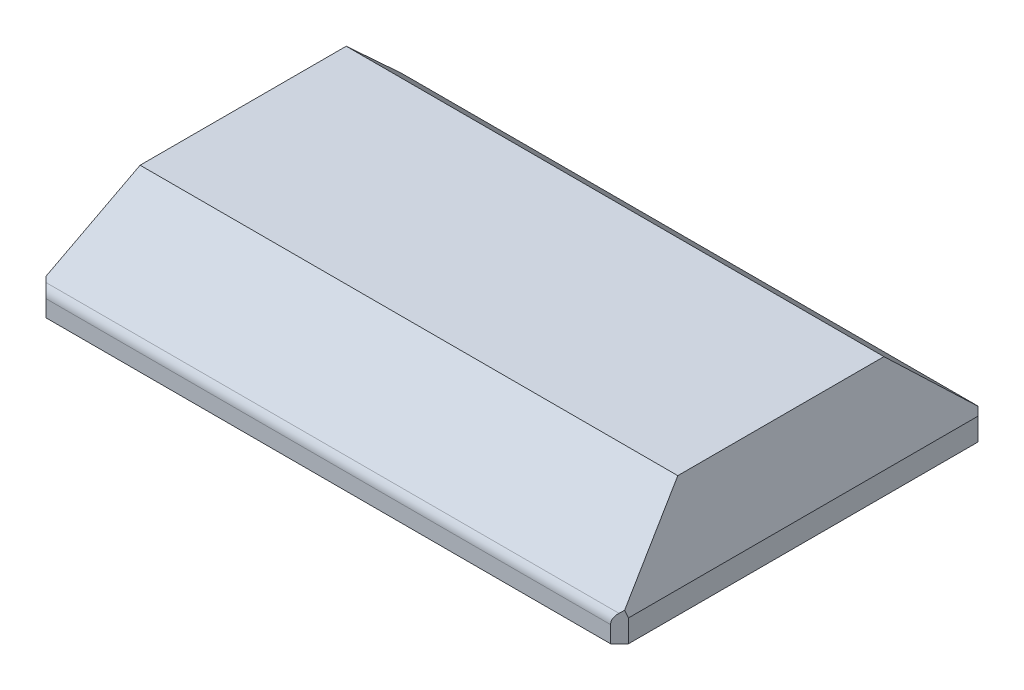
SolidWorks part; units mm, degrees
ref_plane "Front Plane" through (0, 0, 0) normal (0, 0, 1) x (1, 0, 0)
ref_plane "Top Plane" through (0, 0, 0) normal (0, 1, 0) x (1, 0, 0)
ref_plane "Right Plane" through (0, 0, 0) normal (1, 0, 0) x (0, 0, -1)
sketch "Sketch1" plane through (0, 0, 0) normal (0, 1, 0) x (1, 0, 0)
  line L1 (-65, -41) -> (65, -41)
  line L2 (-65, -41) -> (-65, 41)
  line L3 (-65, 41) -> (65, 41)
  line L4 (65, -41) -> (65, 41)
  line L5 (-65, -41) -> (65, 41) construction
  line L6 (-65, 41) -> (65, -41) construction
  point P0 (0, 0)
  dimension "D1" = 130
  dimension "D2" = 82
ref_plane "Plane1" through (0, 22, 0) normal (0, 1, 0) x (1, 0, 0)
sketch "Sketch2" plane through (0, 22, 0) normal (0, 1, 0) x (1, 0, 0)
  line L1 (-60, -23) -> (60, -23)
  line L2 (-60, -23) -> (-60, 23)
  line L3 (-60, 23) -> (60, 23)
  line L4 (60, -23) -> (60, 23)
  line L5 (-60, -23) -> (60, 23) construction
  line L6 (-60, 23) -> (60, -23) construction
  point P0 (0, 0)
  dimension "D1" = 46
  dimension "D2" = 120
extrude "Boss-Extrude1" add sketch "Sketch1" along normal blind 5
sketch "Sketch3" plane through (0, 5, 0) normal (0, 1, 0) x (1, 0, 0)
  line L4 (65, -41) -> (65, 41)
  line L5 (65, 41) -> (-65, 41)
  line L6 (-65, 41) -> (-65, -41)
  line L7 (-65, -41) -> (65, -41)
  line L8 (65, -41) -> (65, 41)
  line L9 (65, 41) -> (-65, 41)
  line L10 (-65, 41) -> (-65, -41)
  line L11 (-65, -41) -> (65, -41)
  dimension "D1" = 0
loft "Loft2" add profiles "Sketch3", "Sketch2"
chamfer "Chamfer1" distance 2 angle 45 4 edges at (-65, 2.5, 41) (65, 2.5, 41) (65, 2.5, -41) (-65, 2.5, -41)
sketch "Sketch4" plane through (0, 0, 0) normal (0, -1, 0) x (1, 0, 0)
  line L0 (0, 41) -> (0, -41) construction
  line L1 (-63, 41) -> (63, 41) construction
  line L2 (63, -41) -> (-63, -41) construction
  line L3 (-40, -37.5) -> (40, -37.5) construction
  circle A0 centre (40, -37.5) radius 1.2
  circle A1 centre (-40, -37.5) radius 1.2
  point P9 (0, -37.5)
  dimension "D3" = 2.4
  dimension "D1" = 3.5
  dimension "D2" = 80
extrude "Cut-Extrude1" cut sketch "Sketch4" against normal blind 6
sketch "Sketch5" plane through (0, 0, 0) normal (0, -1, 0) x (1, 0, 0)
  line L1 (-57, -20) -> (57, -20)
  line L2 (-57, -20) -> (-57, 20)
  line L3 (-57, 20) -> (57, 20)
  line L4 (57, -20) -> (57, 20)
  line L5 (-57, -20) -> (57, 20) construction
  line L6 (-57, 20) -> (57, -20) construction
  point P0 (0, 0)
  dimension "D1" = 40
  dimension "D2" = 114
extrude "Cut-Extrude2" cut sketch "Sketch5" against normal offset from surface (21 mm away) 1 up to face at (0, 22, 0)
mirror "Mirror1" about plane through (0, 0, 0) normal (0, 0, 1) of "Cut-Extrude1"
sketch "Sketch6" plane through (0, 0, 0) normal (0, -1, 0) x (1, 0, 0)
  line L0 (-57, 20) -> (-57, -20) construction
  line L1 (-59, -28) -> (59, -28)
  line L2 (-59, -28) -> (-59, 28)
  line L3 (-59, 28) -> (59, 28)
  line L4 (59, -28) -> (59, 28)
  line L5 (-59, -28) -> (59, 28) construction
  line L6 (-59, 28) -> (59, -28) construction
  line L7 (-57, 20) -> (57, 20) construction
  point P0 (0, 0)
  dimension "D1" = 2
  dimension "D2" = 8
extrude "Cut-Extrude3" cut sketch "Sketch6" against normal blind 12
ref_plane "Plane2" through (0, 4, 0) normal (0, -1, 0) x (-1, 0, 0)
sketch "Sketch8" plane through (0, 4, 0) normal (0, -1, 0) x (-1, 0, 0)
  line L0 (0, 28) -> (0, -41) construction
  line L1 (-59, 28) -> (-52, 28)
  line L2 (-59, 28) -> (-59, 21)
  line L3 (-59, 21) -> (-52, 21)
  line L4 (-52, 28) -> (-52, 21)
  line L5 (59, 28) -> (-59, 28) construction
  line L6 (63, -41) -> (-63, -41) construction
  line L7 (59, 0) -> (-59, 0) construction
  line L8 (59, -28) -> (59, 28) construction
  line L9 (-59, 28) -> (-59, -28) construction
  line L10 (-52, -28) -> (-52, -21)
  line L11 (-59, -21) -> (-52, -21)
  line L12 (-59, -28) -> (-59, -21)
  line L13 (-59, -28) -> (-52, -28)
  line L14 (59, -28) -> (52, -28)
  line L15 (59, -28) -> (59, -21)
  line L16 (59, -21) -> (52, -21)
  line L17 (52, -28) -> (52, -21)
  line L18 (52, 28) -> (52, 21)
  line L19 (59, 21) -> (52, 21)
  line L20 (59, 28) -> (59, 21)
  line L21 (59, 28) -> (52, 28)
  dimension "D1" = 7
extrude "Boss-Extrude2" add sketch "Sketch8" against normal up to surface (8 mm away) up to face at (0, 12, 0)
sketch "Sketch9" plane through (0, 4, 0) normal (0, -1, 0) x (1, 0, 0)
  line L0 (0, 28) -> (0, -41) construction
  line L1 (52, 28) -> (-52, 28) construction
  line L2 (63, -41) -> (-63, -41) construction
  line L3 (59, 0) -> (-59, 0) construction
  line L4 (59, -28) -> (59, 28) construction
  line L5 (-59, 28) -> (-59, -28) construction
  line L6 (-59, 28) -> (-52, 21) construction
  circle A0 centre (-55.5, 24.5) radius 2.1
  circle A1 centre (55.5, 24.5) radius 2.1
  circle A2 centre (55.5, -24.5) radius 2.1
  circle A3 centre (-55.5, -24.5) radius 2.1
  dimension "D1" = 4.2
extrude "Cut-Extrude4" cut sketch "Sketch9" against normal up to surface (8 mm away) up to face at (0, 12, 0)
sketch "Sketch10" plane through (0, 12, 0) normal (0, -1, 0) x (1, 0, 0)
  line L0 (-59, 28) -> (-59, -28) construction
  line L1 (-57, 20) -> (-59, 20)
  line L2 (-57, 20) -> (-57, -20)
  line L3 (-57, -20) -> (-59, -20)
  line L4 (-59, 20) -> (-59, -20)
  line L5 (59, -21) -> (59, 21) construction
  line L6 (57, -20) -> (59, -20)
  line L7 (57, -20) -> (57, 20)
  line L8 (57, 20) -> (59, 20)
  line L9 (59, -20) -> (59, 20)
  line L10 (-57, 20) -> (57, 20) construction
  line L11 (-57, -20) -> (57, -20) construction
extrude "Cut-Extrude5" cut sketch "Sketch10" against normal up to surface (9 mm away) up to face at (0, 21, 0)
fillet "Fillet1" radius 3 2 edges at (0, 5, 41) (0, 5, -41)
